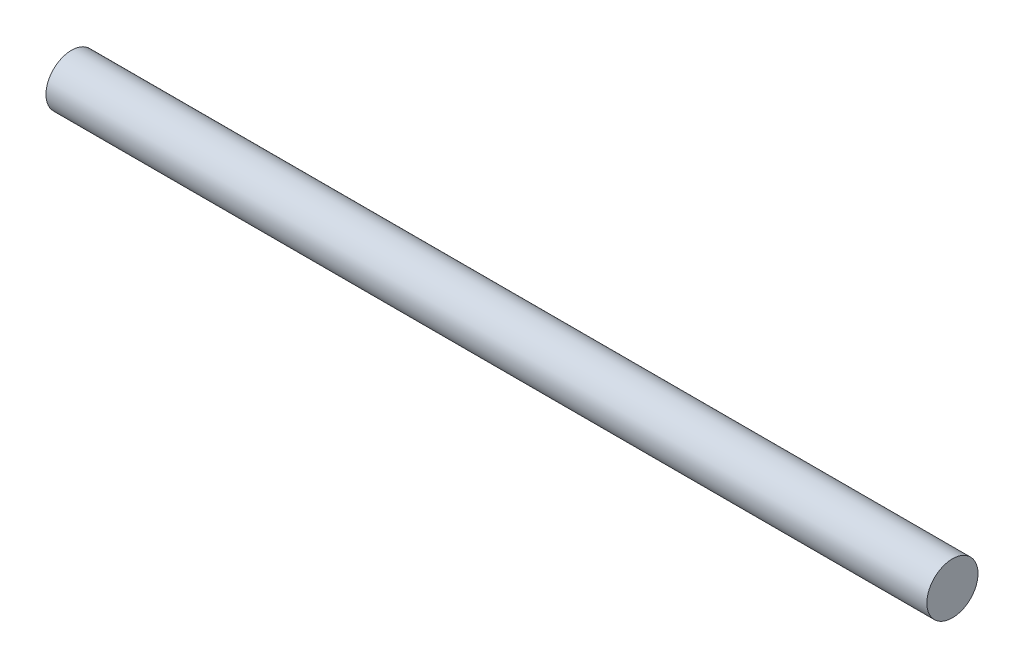
SolidWorks part; units mm, degrees
ref_plane "Plan de face" through (0, 0, 0) normal (0, 0, 1) x (1, 0, 0)
ref_plane "Plan de dessus" through (0, 0, 0) normal (0, 1, 0) x (1, 0, 0)
ref_plane "Plan de droite" through (0, 0, 0) normal (1, 0, 0) x (0, 0, -1)
sketch "Esquisse5" plane through (0, 0, 0) normal (1, 0, 0) x (0, 0, -1)
  circle A0 centre (0, 0) radius 18
extrude "Boss.-Extru.3" add sketch "Esquisse5" along normal blind 620
ref_plane "Plan2" through (10, 0, 0) normal (-1, 0, 0) x (0, 0, 1)
ref_plane "Plan4" through (610, 0, 0) normal (-1, 0, 0) x (0, 0, 1)
sketch "Esquisse6" plane through (10, 0, 0) normal (-1, 0, 0) x (0, 0, 1)
  circle A0 centre (0, 0) radius 18
sketch "Esquisse7" plane through (610, 0, 0) normal (-1, 0, 0) x (0, 0, 1)
  circle A0 centre (0, 0) radius 18
ref_plane "Plan31" through (570, 0, 0) normal (-1, 0, 0) x (0, 0, 1)
sketch "Esquisse32" plane through (570, 0, 0) normal (-1, 0, 0) x (0, 0, 1)
  circle A0 centre (0, 0) radius 18
ref_plane "Plan32" through (370, 0, 0) normal (-1, 0, 0) x (0, 0, 1)
sketch "Esquisse38" plane through (370, 0, 0) normal (-1, 0, 0) x (0, 0, 1)
  circle A0 centre (0, 0) radius 18
ref_plane "Plan41" through (250, 0, 0) normal (-1, 0, 0) x (0, 0, 1)
ref_plane "Plan42" through (50, 0, 0) normal (-1, 0, 0) x (0, 0, 1)
sketch "Esquisse39" plane through (250, 0, 0) normal (-1, 0, 0) x (0, 0, 1)
  circle A0 centre (0, 0) radius 18
sketch "Esquisse40" plane through (50, 0, 0) normal (-1, 0, 0) x (0, 0, 1)
  circle A0 centre (0, 0) radius 18
